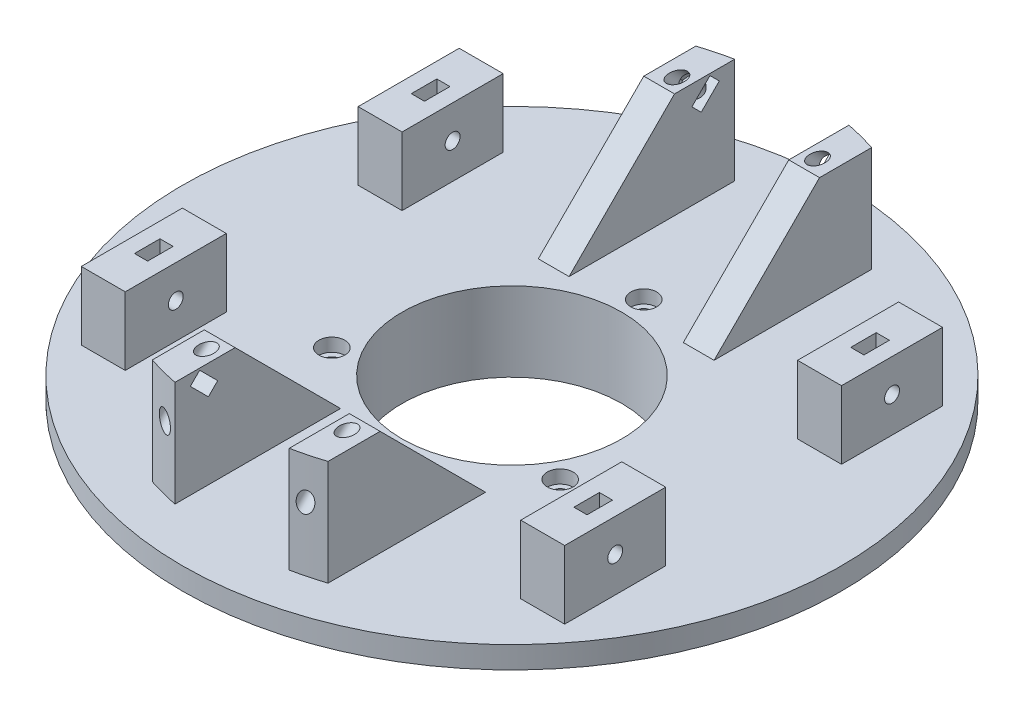
SolidWorks part; units mm, degrees
material "PLA"
ref_plane "Alzado" through (0, 0, 0) normal (0, 0, 1) x (1, 0, 0)
ref_plane "Planta" through (0, 0, 0) normal (0, 1, 0) x (1, 0, 0)
ref_plane "Vista lateral" through (0, 0, 0) normal (1, 0, 0) x (0, 0, -1)
sketch "Croquis1" plane through (0, 0, 0) normal (0, 0, 1) x (1, 0, 0)
  line L0 (25, 0) -> (25, 18)
  line L1 (25, 18) -> (75, 18)
  line L2 (75, 18) -> (75, 13)
  line L3 (75, 13) -> (47, 13)
  line L4 (47, 13) -> (47, 6)
  line L5 (47, 6) -> (35, 6)
  line L6 (35, 6) -> (35, 0)
  line L7 (35, 0) -> (25, 0)
  line L8 (0, 49.6851) -> (0, -18.5516) construction
  dimension "D1" = 75
  dimension "D2" = 47
  dimension "D3" = 35
  dimension "D4" = 25
  dimension "D5" = 6
  dimension "D6" = 7
  dimension "D7" = 5
revolve "Revolución1" add sketch "Croquis1" angle 360 about L8
sketch "Croquis2" plane through (0, 18, 0) normal (0, 1, 0) x (1, 0, 0)
  line L1 (-45, -43) -> (-55, -43)
  line L2 (-45, -43) -> (-45, -20)
  line L3 (-45, -20) -> (-55, -20)
  line L4 (-55, -43) -> (-55, -20)
  line L5 (-45, -43) -> (-55, -20) construction
  line L6 (-45, -20) -> (-55, -43) construction
  point P0 (-50, -31.5)
  dimension "D1" = 20
  dimension "D2" = 10
  dimension "D3" = 23
  dimension "D4" = 45
extrude "Saliente-Extruir1" add sketch "Croquis2" along normal blind 15.5
sketch "Croquis3" plane through (-55, 0, 0) normal (-1, 0, 0) x (0, 0, 1)
  line L0 (20, 33.5) -> (43, 18.5) construction
  line L1 (43, 18.5) -> (43, 33.5) construction
  line L2 (75, 18) -> (-75, 18) construction
  circle A0 centre (31.5, 26) radius 1.7
  dimension "D1" = 3.4
  dimension "D2" = 0.5
extrude "Cortar-Extruir1" cut sketch "Croquis3" against normal blind 15
ref_plane "Plano1" through (-50, 0, 0) normal (-1, 0, 0) x (0, 0, 1)
sketch "Croquis4" plane through (-50, 0, 0) normal (-1, 0, 0) x (0, 0, 1)
  line L0 (28.5988, 27.175) -> (28.5988, 37.175)
  line L1 (31.5, 22.65) -> (34.4012, 24.325)
  line L2 (34.4012, 24.325) -> (34.4012, 27.175)
  line L5 (28.5988, 27.175) -> (28.5988, 24.325)
  line L6 (28.5988, 24.325) -> (31.5, 22.65)
  line L7 (28.5988, 37.175) -> (34.4012, 37.175)
  line L8 (34.4012, 37.175) -> (34.4012, 27.175)
  line L9 (20, 33.5) -> (20, 18) construction
  line L10 (31.5, 29.35) -> (28.5988, 27.675) [skipped]
  line L11 (34.4012, 27.675) -> (31.5, 29.35) [skipped]
  circle A0 centre (31.5, 26) radius 3.35 construction
  dimension "D1" = 6.7
  dimension "D2" = 10
extrude "Cortar-Extruir2" cut sketch "Croquis4" against normal blind 1.5 and the other way blind 1.5
mirror "Simetría1" about plane through (0, 0, 0) normal (1, 0, 0) of "Saliente-Extruir1", "Cortar-Extruir2", "Cortar-Extruir1"
mirror "Simetría2" about plane through (0, 0, 0) normal (0, 0, 1) of "Simetría1", "Saliente-Extruir1", "Cortar-Extruir1", "Cortar-Extruir2"
sketch "Croquis5" plane through (0, 18, 0) normal (0, 1, 0) x (1, 0, 0)
  circle A0 centre (0, 30) radius 1.7
  dimension "D2" = 3.4
  dimension "D1" = 30
extrude "Cortar-Extruir3" cut sketch "Croquis5" against normal blind 40.5
sketch "Croquis6" plane through (0, 18, 0) normal (0, 1, 0) x (1, 0, 0)
  circle A0 centre (0, 30) radius 2.95
  dimension "D1" = 5.9
extrude "Cortar-Extruir4" cut sketch "Croquis6" against normal blind 3
pattern_circular "MatrizC1" count 3 over 360 about axis through (0, 0, 0) along (0, 1, 0) of "Cortar-Extruir4", "Cortar-Extruir3"
sketch "Croquis7" plane through (0, 18, 0) normal (0, 1, 0) x (1, 0, 0)
  line L0 (13, 63.6867) -> (13, 26)
  line L4 (20, 26) -> (20, 61.8466)
  line L5 (13, 26) -> (20, 26)
  arc A0 (20, 61.8466) -> (13, 63.6867) centre (0, 0) ccw
  dimension "D2" = 65
  dimension "D1" = 26
  dimension "D3" = 7
  dimension "D6" = 13
extrude "Saliente-Extruir2" add sketch "Croquis7" along normal blind 24
sketch "Croquis8" plane through (13, 0, 0) normal (-1, 0, 0) x (0, 0, 1)
  line L0 (-26, 18) -> (-71, 63)
  line L1 (-71, 63) -> (-26, 63)
  line L2 (-26, 63) -> (-26, 18)
  line L3 (-63.6867, 18) -> (-26, 18) construction
  dimension "D1" = 45
  dimension "D2" = 45
extrude "Cortar-Extruir5" cut sketch "Croquis8" against normal blind 10
sketch "Croquis9" plane through (0, -4, -4) normal (0, 0.7071, 0.7071) x (1, 0, 0)
  line L1 (20, 65.0538) -> (13, 65.0538) construction
  circle A0 centre (16, 67.5538) radius 1.7
  dimension "D1" = 3.4
  dimension "D2" = 2.5
  dimension "D3" = 16
extrude "Cortar-Extruir6" cut sketch "Croquis9" against normal blind 20
ref_plane "Plano2" through (0, -10.364, -10.364) normal (0, 0.7071, 0.7071) x (1, 0, 0)
sketch "Croquis10" plane through (0, -10.364, -10.364) normal (0, 0.7071, 0.7071) x (1, 0, 0)
  line L0 (20, 65.0538) -> (13, 65.0538) construction
  line L1 (17.675, 64.6526) -> (19.35, 67.5538)
  line L2 (19.35, 67.5538) -> (17.675, 70.455)
  line L3 (17.675, 70.455) -> (14.325, 70.455)
  line L4 (14.325, 70.455) -> (12.65, 67.5538) construction
  line L5 (12.65, 67.5538) -> (14.325, 64.6526) construction
  line L6 (14.325, 64.6526) -> (17.675, 64.6526)
  line L7 (14.325, 70.455) -> (7.675, 70.455)
  line L8 (7.675, 70.455) -> (7.675, 64.6526)
  line L9 (7.675, 64.6526) -> (14.325, 64.6526)
  circle A0 centre (16, 67.5538) radius 3.35 construction
  circle A2 centre (16, 67.5538) radius 1.7 construction
  dimension "D1" = 6.7
  dimension "D2" = 10
extrude "Cortar-Extruir7" cut sketch "Croquis10" along normal blind 3
mirror "Simetría3" about plane through (0, 0, 0) normal (1, 0, 0) of "Cortar-Extruir7", "Cortar-Extruir5", "Saliente-Extruir2", "Cortar-Extruir6"
mirror "Simetría4" about plane through (0, 0, 0) normal (0, 0, 1) of "Simetría3", "Saliente-Extruir2", "Cortar-Extruir5", "Cortar-Extruir6", "Cortar-Extruir7"
